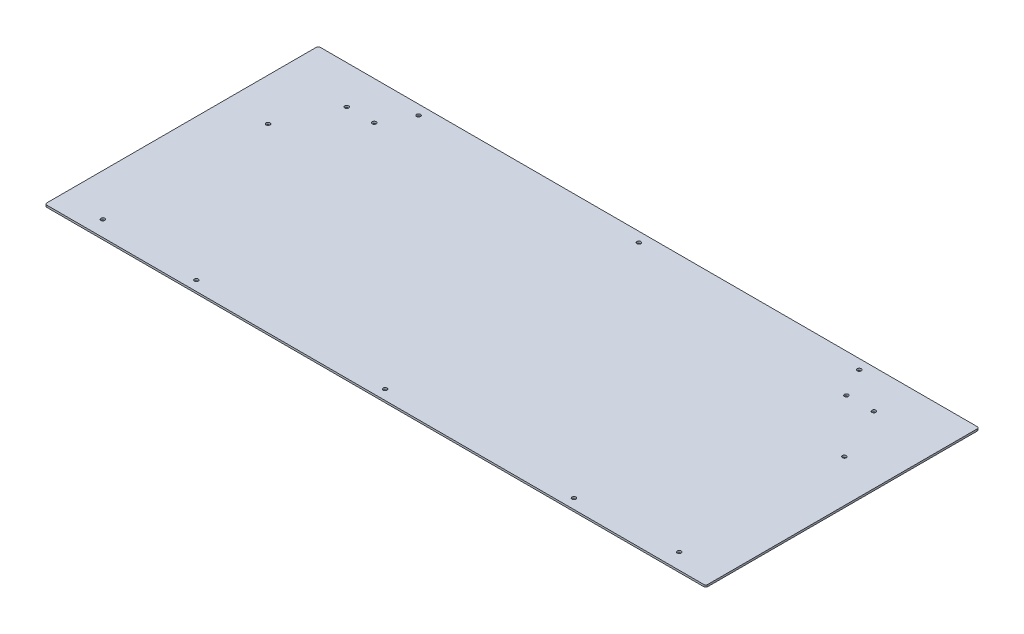
SolidWorks part; units mm, degrees
material "PC High Viscosity"
ref_plane "Front Plane" through (0, 0, 0) normal (0, 0, 1) x (1, 0, 0)
ref_plane "Top Plane" through (0, 0, 0) normal (0, 1, 0) x (1, 0, 0)
ref_plane "Right Plane" through (0, 0, 0) normal (1, 0, 0) x (0, 0, -1)
sketch "Sketch1" plane through (0, 0, 0) normal (0, 1, 0) x (1, 0, 0)
  line L1 (0, 0) -> (1066.8, 0)
  line L2 (0, 0) -> (0, 441.325)
  line L3 (0, 441.325) -> (1066.8, 441.325)
  line L4 (1066.8, 0) -> (1066.8, 441.325)
  dimension "D1" = 441.325
  dimension "D2" = 1066.8
extrude "Boss-Extrude1" add sketch "Sketch1" along normal blind 3.175
sketch "Sketch2" plane through (0, 3.175, 0) normal (0, 1, 0) x (1, 0, 0)
  line L0 (0, 220.6625) -> (1066.8, 220.6625) construction
  line L1 (0, 441.325) -> (0, 0) construction
  line L2 (1066.8, 0) -> (1066.8, 441.325) construction
  line L3 (533.4, 441.325) -> (533.4, 0) construction
  line L4 (1066.8, 441.325) -> (0, 441.325) construction
  line L5 (0, 0) -> (1066.8, 0) construction
  line L6 (0, 441.325) -> (0, 365.125)
  line L7 (0, 0) -> (127, 0)
  line L8 (0, 0) -> (0, 76.2)
  line L9 (0, 76.2) -> (127, 76.2)
  line L10 (127, 0) -> (127, 76.2)
  line L11 (0, 365.125) -> (127, 365.125)
  line L12 (0, 441.325) -> (127, 441.325)
  line L13 (127, 441.325) -> (127, 365.125)
  line L14 (939.8, 441.325) -> (939.8, 365.125)
  line L15 (1066.8, 441.325) -> (939.8, 441.325)
  line L16 (1066.8, 365.125) -> (939.8, 365.125)
  line L17 (939.8, 0) -> (939.8, 76.2)
  line L18 (1066.8, 76.2) -> (939.8, 76.2)
  line L19 (1066.8, 0) -> (1066.8, 76.2)
  line L20 (1066.8, 0) -> (939.8, 0)
  line L21 (1066.8, 441.325) -> (1066.8, 365.125)
  dimension "D1" = 127
  dimension "D2" = 76.2
extrude "Cut-Extrude1" [suppressed] cut sketch "Sketch2" against normal through all
hole_wizard "1/4 (0.25) Diameter Hole1" positions "Sketch3" profile "Sketch4" hole size "1/4" standard "ANSI Inch" end condition through all
sketch "Sketch3" plane through (0, 3.175, 0) normal (0, 1, 0) x (1, 0, 0)
  line L0 (533.4, 441.325) -> (533.4, 0) construction
  line L1 (1066.8, 441.325) -> (0, 441.325) construction
  line L2 (0, 0) -> (1066.8, 0) construction
  line L4 (0, 220.6625) -> (1066.8, 220.6625) construction
  line L5 (0, 441.325) -> (0, 0) construction
  line L6 (1066.8, 0) -> (1066.8, 441.325) construction
  line L7 (1066.8, 441.325) -> (0, 441.325) construction
  line L9 (0, 441.325) -> (0, 0) construction
  line L10 (958.85, 379.3744) -> (914.4, 379.3744) construction
  line L11 (1066.8, 0) -> (1066.8, 441.325) construction
  point P0 (228.6, 15.875)
  point P2 (533.4, 15.875)
  point P4 (838.2, 15.875)
  point P28 (889, 425.45)
  point P29 (533.4, 425.45)
  point P30 (177.8, 425.45)
  point P37 (68.2625, 25.4)
  point P39 (68.2625, 292.1)
  point P48 (998.5375, 25.4)
  point P49 (998.5375, 292.1)
  point P50 (958.85, 379.3744)
  point P52 (914.4, 379.3744)
  point P58 (941.8638, 382.3069)
  point P61 (0, 0)
  point P62 (107.95, 379.3744)
  point P63 (152.4, 379.3744)
  dimension "D1" = 304.8
  dimension "D2" = 15.875
  dimension "D3" = 355.6
  dimension "D5" = 15.875
  dimension "D6" = 149.225
  dimension "D4" = 68.2625
  dimension "D7" = 266.7
  dimension "D8" = 44.45
  dimension "D9" = 107.95
  dimension "D10" = 61.9506
sketch "Sketch4" plane through (228.6, 3.175, -15.875) normal (1, 0, 0) x (0, 0, 1)
  line L0 (0, 0) -> (0, 3.175)
  line L1 (0, 3.175) -> (3.175, 3.175)
  line L2 (3.175, 3.175) -> (3.175, 0)
  line L5 (3.175, 0) -> (0, 0)
  line L11 (0, -6.35) -> (0, 107.95) construction
  dimension "Thru Hole Dia." = 6.35
  dimension "Thru Hole Depth" = 3.175
hole_wizard "1/4 (0.25) Diameter Hole2" [suppressed] positions "Sketch5" profile "Sketch6" hole size "1/4" standard "ANSI Inch"
sketch "Sketch5" plane through (0, 3.175, 0) normal (0, 1, 0) x (1, 0, 0)
  line L0 (0, 222.25) -> (1066.8, 222.25) construction
  line L1 (0, 444.5) -> (0, 0) construction
  line L2 (1066.8, 0) -> (1066.8, 444.5) construction
  line L4 (533.4, 444.5) -> (533.4, 0) construction
  line L5 (1066.8, 444.5) -> (0, 444.5) construction
  line L6 (0, 0) -> (1066.8, 0) construction
  line L7 (1066.8, 444.5) -> (0, 444.5) construction
  point P0 (68.2625, 25.4)
  point P2 (68.2625, 292.1)
  point P24 (998.5375, 25.4)
  point P25 (998.5375, 292.1)
  dimension "D1" = 152.4
  dimension "D2" = 68.2625
  dimension "D3" = 266.7
sketch "Sketch6" plane through (68.2625, 3.175, -25.4) normal (1, 0, 0) x (0, 0, 1)
  line L0 (0, 0) -> (0, 3.175)
  line L1 (0, 3.175) -> (3.175, 3.175)
  line L2 (3.175, 3.175) -> (3.175, 0)
  line L5 (3.175, 0) -> (0, 0)
  line L11 (0, -6.35) -> (0, 107.95) construction
  dimension "Thru Hole Dia." = 6.35
  dimension "Thru Hole Depth" = 3.175
fillet "Fillet2" radius 3.175 4 edges at (1066.8, 1.5875, -441.325) (1066.8, 1.5875, 0) (0, 1.5875, 0) (0, 1.5875, -441.325)
equation "\"D5@Sketch3\"=\"D2@Sketch3\""
